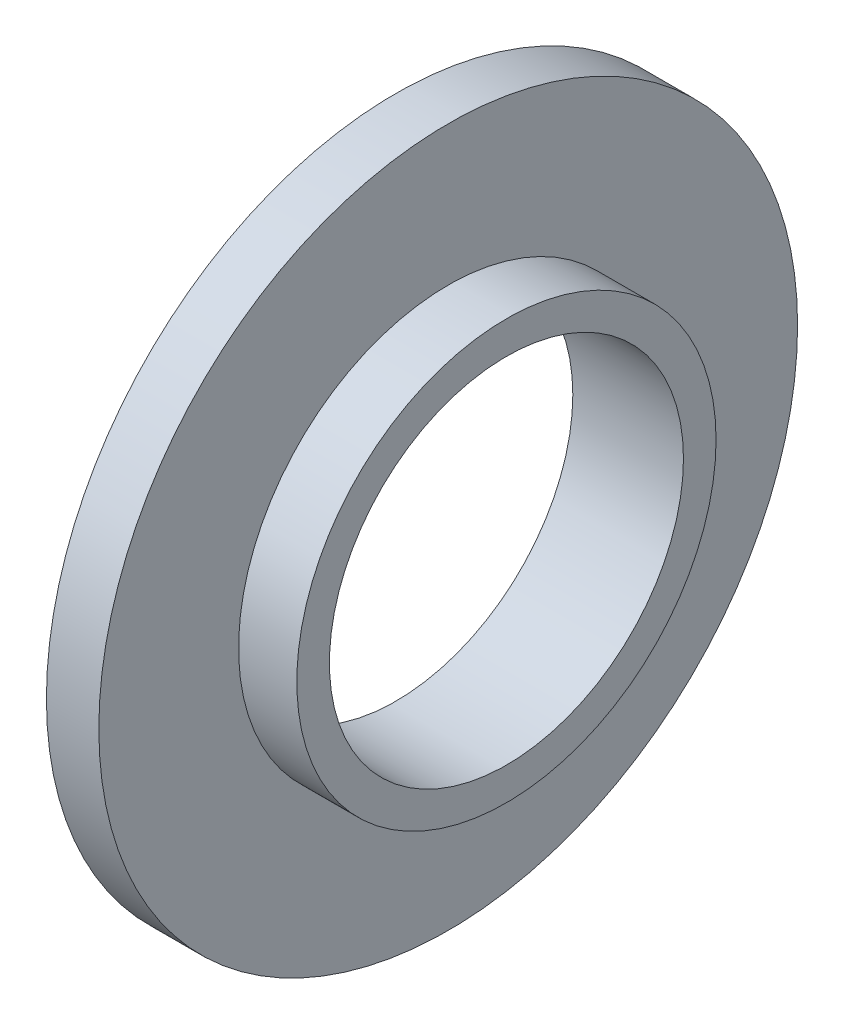
SolidWorks part; units mm, degrees
ref_plane "前视基准面" through (0, 0, 0) normal (0, 0, 1) x (1, 0, 0)
ref_plane "上视基准面" through (0, 0, 0) normal (0, 1, 0) x (1, 0, 0)
ref_plane "右视基准面" through (0, 0, 0) normal (1, 0, 0) x (0, 0, -1)
sketch "草图1" plane through (0, 0, 0) normal (1, 0, 0) x (0, 0, -1)
  circle A0 centre (0, 0) radius 30
extrude "凸台-拉伸1" add sketch "草图1" along normal blind 4.5
sketch "草图2" plane through (4.5, 0, 0) normal (1, 0, 0) x (0, 0, -1)
  circle A0 centre (0, 0) radius 18
extrude "凸台-拉伸2" add sketch "草图2" along normal blind 5
sketch "草图3" plane through (9.5, 0, 0) normal (1, 0, 0) x (0, 0, -1)
  circle A0 centre (0, 0) radius 15.2
extrude "切除-拉伸1" cut sketch "草图3" against normal through all
